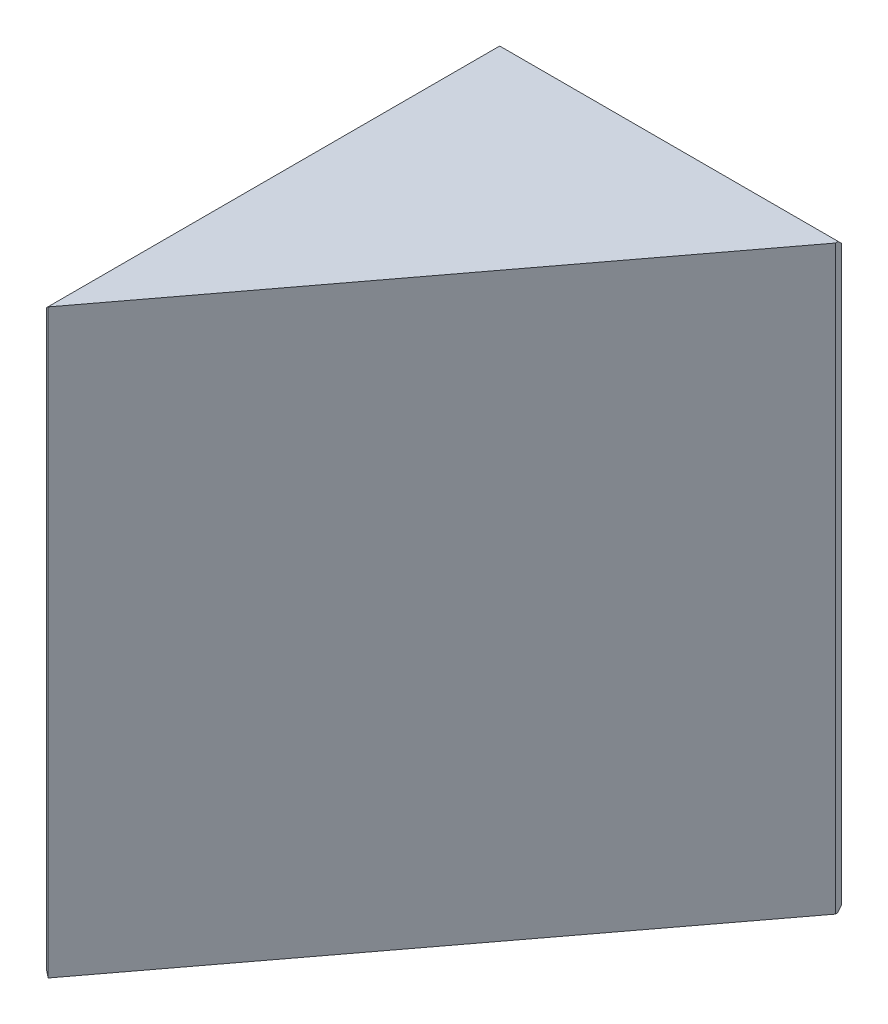
SolidWorks part; units mm, degrees
material "Стекло"
ref_plane "Спереди" through (0, 0, 0) normal (0, 0, 1) x (1, 0, 0)
ref_plane "Сверху" through (0, 0, 0) normal (0, 1, 0) x (1, 0, 0)
ref_plane "Справа" through (0, 0, 0) normal (1, 0, 0) x (0, 0, -1)
sketch "Эскиз1" plane through (0, 0, 0) normal (0, 1, 0) x (1, 0, 0)
  line L0 (0, 0) -> (11.9829, 15.9019)
  line L1 (11.9829, 15.9019) -> (0, 15.9019)
  line L2 (0, 15.9019) -> (0, 0)
  line L3 (5.5, -29.5981) -> (5.5, 26.0735) construction
  dimension "D1" = 9.57
  dimension "D2" = 53
extrude "Вытянуть1" add sketch "Эскиз1" along normal blind 20
chamfer "Фаска1" distance 0.3 angle 60 1 edges at (0, 10, 0)
chamfer "Фаска2" distance 0.3 angle 45 1 edges at (11.9829, 10, -15.9019)
chamfer "Фаска3" distance 0.15 angle 45 5 edges at (5.8844, 0, -15.9019) (5.8844, 20, -15.9019) (0, 0, -8.1009) (0, 20, -8.1009) (0, 10, -15.9019)
